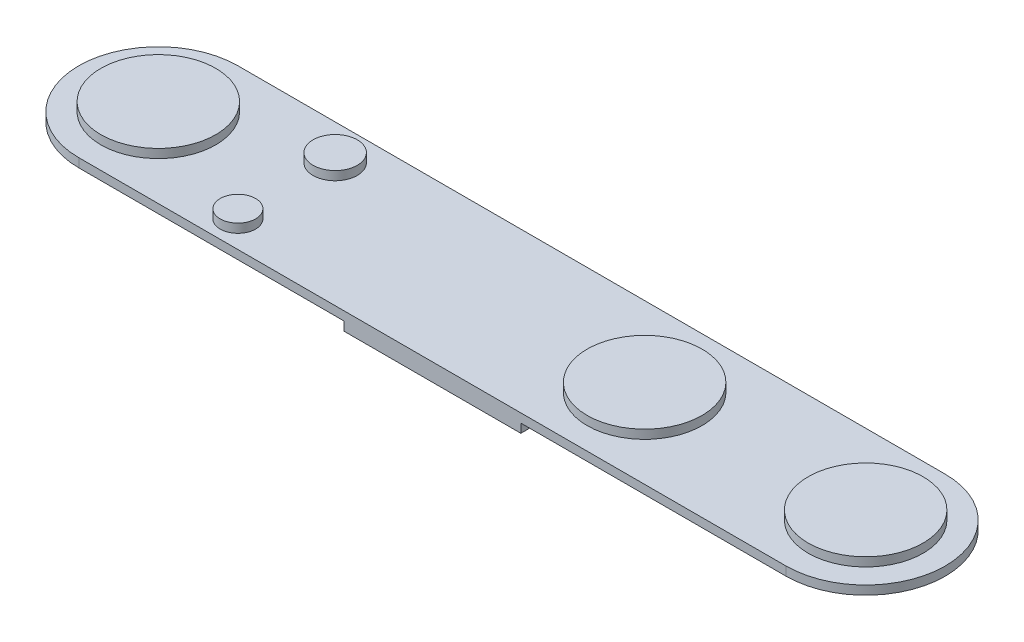
SolidWorks part; units mm, degrees
ref_plane "Plano frontal" through (0, 0, 0) normal (0, 0, 1) x (1, 0, 0)
ref_plane "Plano superior" through (0, 0, 0) normal (0, 1, 0) x (1, 0, 0)
ref_plane "Plano direito" through (0, 0, 0) normal (1, 0, 0) x (0, 0, -1)
sketch "Esboço1" plane through (0, 0, 0) normal (0, 1, 0) x (1, 0, 0)
  line L0 (-40, 0) -> (40, 0) construction
  line L1 (-40, 9) -> (40, 9)
  line L2 (-40, -9) -> (40, -9)
  arc A0 (-40, 9) -> (-40, -9) centre (-40, 0) ccw
  arc A1 (40, -9) -> (40, 9) centre (40, 0) ccw
  point P2 (0, 0)
  dimension "D2" = 18
  dimension "D1" = 80
extrude "Ressalto-extrusão1" add sketch "Esboço1" along normal blind 1
sketch "Esboço2" plane through (0, 1, 0) normal (0, 1, 0) x (1, 0, 0)
  line L0 (-49, 0) -> (49, 0) construction
  line L1 (40, 9) -> (40, -9) construction
  line L2 (-40, 9) -> (-40, -9) construction
  line L3 (-25, 9) -> (-25, -9) construction
  line L4 (40, 9) -> (-40, 9) construction
  line L5 (-40, -9) -> (40, -9) construction
  arc A0 (-40, 9) -> (-40, -9) centre (-40, 0) ccw construction
  arc A1 (40, -9) -> (40, 9) centre (40, 0) ccw construction
  circle A3 centre (-25, 5) radius 2.5
  circle A4 centre (-25, -6) radius 2
  circle A5 centre (15, 0) radius 6.5
  circle A7 centre (40, 0) radius 6.5
  circle A8 centre (-40, 0) radius 6.5
  point P32 (0, 0)
  point P33 (0, 0)
  point P34 (0, 0)
  dimension "D1" = 13
  dimension "D2" = 25
  dimension "D4" = 5
  dimension "D5" = 4
  dimension "D6" = 3
  dimension "D7" = 4
  dimension "D3" = 15
extrude "Ressalto-extrusão2" add sketch "Esboço2" along normal blind 1
sketch "Esboço3" plane through (0, 0, 0) normal (0, -1, 0) x (1, 0, 0)
  line L0 (-40, 9) -> (40, 9) construction
  line L1 (-10, -9) -> (10, -9)
  line L2 (-10, -9) -> (-10, 9)
  line L3 (-10, 9) -> (10, 9)
  line L4 (10, -9) -> (10, 9)
  line L5 (-10, -9) -> (10, 9) construction
  line L6 (-10, 9) -> (10, -9) construction
  point P0 (0, 0)
  dimension "D1" = 20
extrude "Ressalto-extrusão3" add sketch "Esboço3" along normal blind 1
